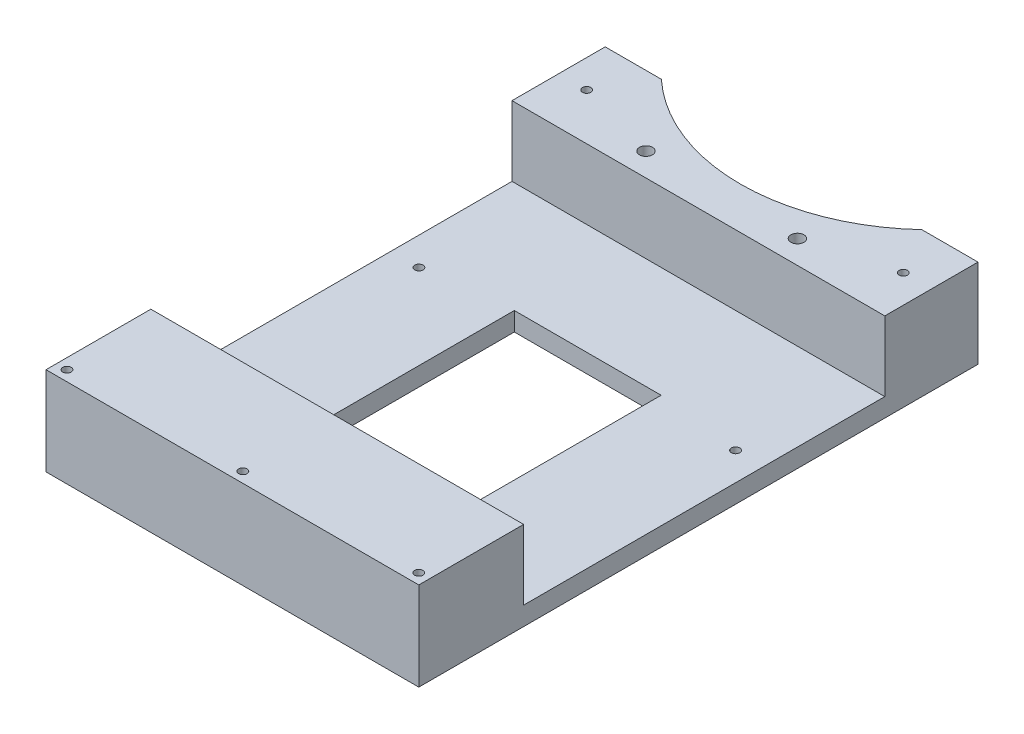
SolidWorks part; units mm, degrees
ref_plane "정면" through (0, 0, 0) normal (0, 0, 1) x (1, 0, 0)
ref_plane "윗면" through (0, 0, 0) normal (0, 1, 0) x (1, 0, 0)
ref_plane "우측면" through (0, 0, 0) normal (1, 0, 0) x (0, 0, -1)
ref_plane "평면1" through (0, 0, 0) normal (0, -1, 0) x (1, 0, 0)
sketch "스케치1" plane through (0, 0, 0) normal (0, -1, 0) x (1, 0, 0)
  line L0 (20.75, 40.75) -> (20.75, -8.75)
  line L1 (20.75, -8.75) -> (-10.75, -8.75)
  line L2 (-10.75, -8.75) -> (-10.75, 40.75)
  line L3 (-10.75, 40.75) -> (20.75, 40.75)
  line L5 (45, -52.5) -> (45, 67.5)
  line L6 (45, 67.5) -> (-35, 67.5)
  line L7 (-35, 67.5) -> (-35, -52.5)
  line L8 (-35, -52.5) -> (-22.9464, -52.5)
  line L9 (32.9464, -52.5) -> (45, -52.5)
  circle A0 centre (-28.975, -41.745) radius 0.9
  circle A1 centre (-28.975, -6.5) radius 0.9
  circle A2 centre (-32.75, 65.25) radius 0.9
  circle A3 centre (5, 65.25) radius 0.9
  circle A4 centre (42.75, 65.25) radius 0.9
  circle A5 centre (38.975, -6.5) radius 0.9
  circle A6 centre (38.975, -41.745) radius 0.9
  arc A8 (32.9464, -52.5) -> (-22.9464, -52.5) centre (5, -82.5) ccw
  dimension "D1" = 80
  dimension "D2" = 24.25
  dimension "D6" = 74
  dimension "D8" = 1.8
  dimension "D9" = 1.8
  dimension "D14" = 1.8
  dimension "D15" = 1.8
  dimension "D18" = 30
  dimension "D19" = 41
  dimension "D16" = 26.75
  dimension "D3" = 120
  dimension "D4" = 74
  dimension "D5" = 6.025
  dimension "D7" = 6.025
  dimension "D10" = 31.5
  dimension "D11" = 49.5
  dimension "D12" = 2.25
  dimension "D13" = 40
extrude "보스-돌출1" add sketch "스케치1" against normal blind 4
sketch "스케치2" plane through (0, 4, 0) normal (0, 1, 0) x (1, 0, 0)
  line L0 (-35, -67.5) -> (-35, 52.5) construction
  line L1 (45, -67.5) -> (-35, -67.5)
  line L2 (45, -67.5) -> (45, -45)
  line L3 (45, -45) -> (-35, -45)
  line L4 (-35, -67.5) -> (-35, -45)
  line L5 (45, 32.5) -> (-35, 32.5)
  line L6 (45, 52.5) -> (45, -67.5) construction
  line L7 (-35, 32.5) -> (-35, 52.5)
  line L8 (-35, 52.5) -> (-22.9464, 52.5)
  line L9 (45, 32.5) -> (45, 52.5)
  line L10 (32.9464, 52.5) -> (45, 52.5)
  arc A0 (-22.9464, 52.5) -> (32.9464, 52.5) centre (5, 82.5) ccw
  point P21 (40.4641, 52.5)
  dimension "D3" = 40
  dimension "D6" = 82
  dimension "D1" = 22.5
  dimension "D2" = 20
  dimension "D5" = 30
extrude "보스-돌출2" add sketch "스케치2" along normal blind 15
sketch "스케치3" plane through (0, 19, 0) normal (0, 1, 0) x (1, 0, 0)
  line L2 (45, 32.5) -> (45, 52.5) construction
  line L5 (-35, 52.5) -> (-35, 32.5) construction
  line L6 (45, 52.5) -> (32.9464, 52.5) construction
  circle A0 centre (38.975, 42.5) radius 0.9
  circle A1 centre (-28.975, 42.5) radius 0.9
  point P8 (45, 47.6944)
  point P11 (-35, 42.5)
  point P14 (-45, 42.5757)
  dimension "D3" = 1.8
  dimension "D4" = 1.8
  dimension "D1" = 10
  dimension "D2" = 6.025
  dimension "D5" = 6.025
extrude "컷-돌출1" cut sketch "스케치3" against normal through all
sketch "스케치4" plane through (0, 0, 0) normal (0, -1, 0) x (1, 0, 0)
  circle A0 centre (42.75, 65.25) radius 0.9
  circle A1 centre (5, 65.25) radius 0.9
  circle A2 centre (-32.75, 65.25) radius 0.9
extrude "컷-돌출2" cut sketch "스케치4" against normal through all
sketch "스케치6" plane through (0, 0, 45) normal (0, 0, -1) x (-1, 0, 0)
  line L0 (-45, 4) -> (35, 4) construction
  line L1 (31, 4) -> (-41, 4)
  line L2 (31, 4) -> (31, 15)
  line L3 (31, 15) -> (-41, 15)
  line L4 (-41, 4) -> (-41, 15)
  line L5 (-45, 19) -> (-45, 4) construction
  line L6 (35, 19) -> (35, 4) construction
  line L7 (-45, 19) -> (35, 19) construction
  point P8 (-45, 11.5)
  dimension "D1" = 4
  dimension "D2" = 4
  dimension "D3" = 4
extrude "컷-돌출3" cut sketch "스케치6" against normal offset from surface (18.5 mm away) 4 up to face at (5, 9.5, 67.5)
sketch "스케치7" plane through (0, 19, 0) normal (0, 1, 0) x (1, 0, 0)
  line L0 (-35, 32.5) -> (45, 32.5) construction
  line L1 (25, 32.5) -> (-15, 32.5) construction
  line L2 (25, 32.5) -> (25, 42.5) construction
  line L3 (25, 42.5) -> (-15, 42.5) construction
  line L4 (-15, 32.5) -> (-15, 42.5) construction
  line L5 (-35, 52.5) -> (-35, 32.5) construction
  circle A0 centre (21.25, 37.5) radius 1.4
  circle A1 centre (-11.25, 37.5) radius 1.4
  dimension "D4" = 2.8
  dimension "D5" = 2.8
  dimension "D7" = 3.75
  dimension "D8" = 5
  dimension "D9" = 5
  dimension "D1" = 40
  dimension "D2" = 20
  dimension "D3" = 10
  dimension "D6" = 3.75
extrude "컷-돌출5" cut sketch "스케치7" against normal blind 8
